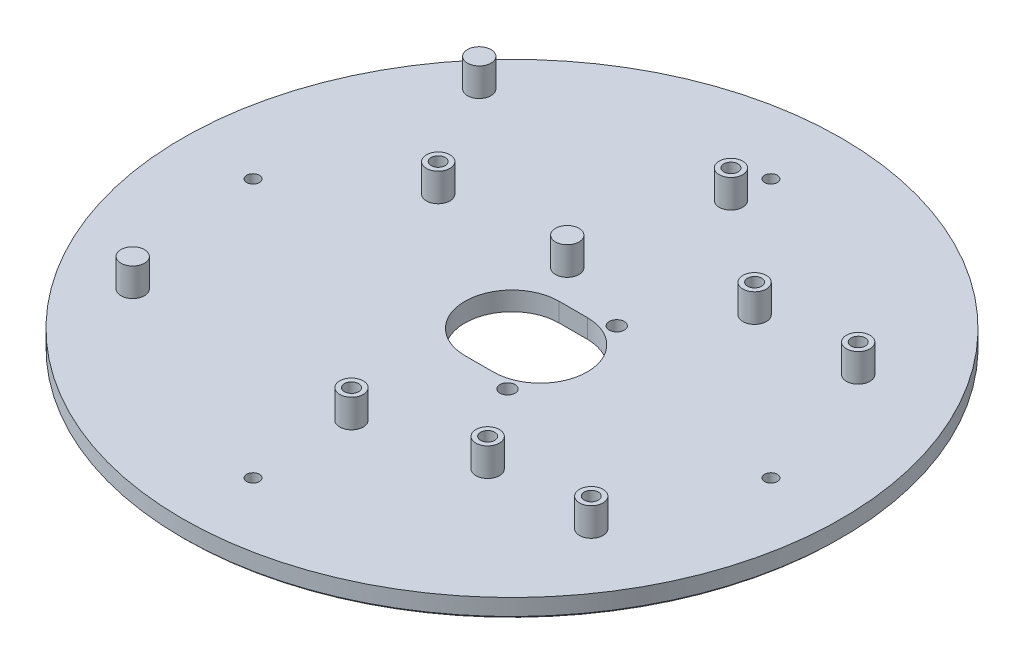
SolidWorks part; units mm, degrees
ref_plane "Ebene vorne" through (0, 0, 0) normal (0, 0, 1) x (1, 0, 0)
ref_plane "Ebene oben" through (0, 0, 0) normal (0, 1, 0) x (1, 0, 0)
ref_plane "Ebene rechts" through (0, 0, 0) normal (1, 0, 0) x (0, 0, -1)
sketch "Skizze1" plane through (0, 0, 0) normal (0, 1, 0) x (1, 0, 0)
  circle A0 centre (0, 0) radius 70
  dimension "D1" = 140
extrude "Aufsatz-Linear austragen1" add sketch "Skizze1" along normal blind 4
sketch "Skizze3" plane through (0, 0, 0) normal (0, -1, 0) x (1, 0, 0)
  line L0 (6, 0) -> (0, 0) construction
  line L1 (6, -10) -> (0, -10)
  line L2 (6, 10) -> (0, 10)
  arc A0 (6, -10) -> (6, 10) centre (6, 0) ccw
  arc A1 (0, 10) -> (0, -10) centre (0, 0) ccw
  point P2 (3, 0)
  point P4 (19.3628, 0)
  dimension "D1" = 20
  dimension "D2" = 6
extrude "Schnitt-Linear austragen1" cut sketch "Skizze3" against normal up to next
sketch "Skizze2" plane through (0, 4, 0) normal (0, 1, 0) x (1, 0, 0)
  circle A0 centre (-32.5332, 16.8549) radius 1.5
  circle A1 centre (-0.2807, 46.78) radius 1.5
  circle A2 centre (23.2607, 28.2715) radius 1.5
  circle A3 centre (45.2607, 28.2715) radius 1.5
  circle A4 centre (45.2607, -28.4285) radius 1.5
  circle A5 centre (23.2607, -28.4285) radius 1.5
  circle A6 centre (-0.153, -33.9402) radius 1.5
  circle A7 centre (-47.534, 40.5718) radius 2.5
  circle A8 centre (-5.2934, 17.0303) radius 2.5
  circle A9 centre (-47.534, -33.0275) radius 2.5
  circle A10 centre (-32.5332, 16.8549) radius 2.5
  circle A11 centre (-0.2807, 46.78) radius 2.5
  circle A12 centre (23.2607, 28.2715) radius 2.5
  circle A13 centre (45.2607, 28.2715) radius 2.5
  circle A14 centre (45.2607, -28.4285) radius 2.5
  circle A15 centre (23.2607, -28.4285) radius 2.5
  circle A16 centre (-0.153, -33.9402) radius 2.5
  dimension "D1" = 3
  dimension "D2" = 5
  dimension "D3" = 1
extrude "Aufsatz-Linear austragen2" add sketch "Skizze2" along normal blind 6 and the other way up to surface (4 mm away) other way up to face at (3, 0, 0)
sketch "Skizze4" plane through (0, 4, 0) normal (0, 1, 0) x (1, 0, 0)
  circle A0 centre (-32.5332, 16.8549) radius 1.5 construction
  circle A1 centre (23.2607, 28.2715) radius 1.5 construction
  circle A2 centre (45.2607, 28.2715) radius 1.5 construction
  circle A3 centre (45.2607, -28.4285) radius 1.5 construction
  circle A4 centre (23.2607, -28.4285) radius 1.5 construction
  circle A5 centre (-0.153, -33.9402) radius 1.5 construction
  circle A6 centre (-0.2807, 46.78) radius 1.4101 construction
  circle A7 centre (-32.5332, 16.8549) radius 1.5
  circle A8 centre (23.2607, 28.2715) radius 1.5
  circle A9 centre (45.2607, 28.2715) radius 1.5
  circle A10 centre (45.2607, -28.4285) radius 1.5
  circle A11 centre (23.2607, -28.4285) radius 1.5
  circle A12 centre (-0.153, -33.9402) radius 1.5
  circle A13 centre (-0.2807, 46.78) radius 1.4101
extrude "Schnitt-Linear austragen2" cut sketch "Skizze4" against normal through all
chamfer "Fase1" distance 0.5 angle 45 1 edges at (0, 0, 70)
sketch "Skizze5" plane through (0, 0, 0) normal (0, -1, 0) x (1, 0, 0)
  line L0 (69.5, 0) -> (-69.5, 0) construction
  circle A0 centre (0, 0) radius 69.5 construction
  circle A1 centre (0, 0) radius 55 construction
  circle A2 centre (-55, 0) radius 1.35
  circle A3 centre (55, 0) radius 1.35
  circle A4 centre (0, -55) radius 1.35
  circle A5 centre (0, 55) radius 1.35
  dimension "D1" = 2.7
  dimension "D2" = 110
extrude "Schnitt-Linear austragen3" cut sketch "Skizze5" against normal up to next
sketch "Skizze6" plane through (0, 0, 0) normal (0, -1, 0) x (-1, 0, 0)
  circle A0 centre (-10.6442, 11.6052) radius 1.6
  circle A1 centre (-10.6442, -11.6052) radius 1.6
  dimension "D1" = 3.2
extrude "Schnitt-Linear austragen4" cut sketch "Skizze6" against normal blind 4
